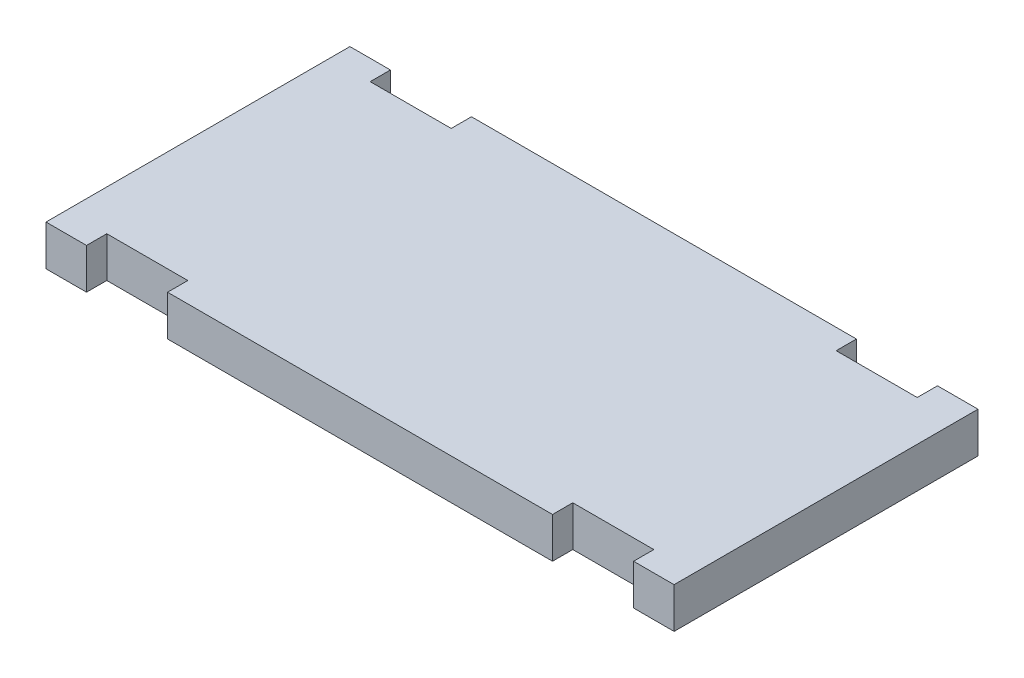
SolidWorks part; units mm, degrees
ref_plane "Front Plane" through (0, 0, 0) normal (0, 0, 1) x (1, 0, 0)
ref_plane "Top Plane" through (0, 0, 0) normal (0, 1, 0) x (1, 0, 0)
ref_plane "Right Plane" through (0, 0, 0) normal (1, 0, 0) x (0, 0, -1)
sketch "Sketch1" plane through (0, 0, 0) normal (0, 1, 0) x (1, 0, 0)
  line L0 (0, 3.75) -> (0, -3.75) construction
  line L1 (-7.75, 3.75) -> (-6.75, 3.75)
  line L2 (-7.75, 3.75) -> (-7.75, -3.75)
  line L3 (-7.75, -3.75) -> (-6.75, -3.75)
  line L4 (7.75, 3.75) -> (7.75, -3.75)
  line L5 (-4.75, 3.75) -> (4.75, 3.75)
  line L6 (4.75, 3.75) -> (4.75, 3.25)
  line L7 (-6.75, 3.75) -> (-6.75, 3.25)
  line L8 (-6.75, 3.25) -> (-4.75, 3.25)
  line L9 (-4.75, 3.75) -> (-4.75, 3.25)
  line L10 (6.75, 3.25) -> (4.75, 3.25)
  line L11 (6.75, 3.75) -> (6.75, 3.25)
  line L12 (-7.75, 0) -> (0, 0) construction
  line L13 (6.75, -3.75) -> (6.75, -3.25)
  line L14 (6.75, -3.25) -> (4.75, -3.25)
  line L15 (4.75, -3.75) -> (4.75, -3.25)
  line L16 (-4.75, -3.75) -> (-4.75, -3.25)
  line L17 (-6.75, -3.25) -> (-4.75, -3.25)
  line L18 (-6.75, -3.75) -> (-6.75, -3.25)
  line L19 (6.75, 3.75) -> (7.75, 3.75)
  line L20 (6.75, -3.75) -> (7.75, -3.75)
  line L21 (-4.75, -3.75) -> (4.75, -3.75)
  point P6 (0, 0)
  dimension "D1" = 7.5
  dimension "D2" = 15.5
  dimension "D3" = 0.5
  dimension "D4" = 2
  dimension "D5" = 1
  dimension "D6" = 9.5
extrude "Boss-Extrude1" add sketch "Sketch1" along normal blind 1
